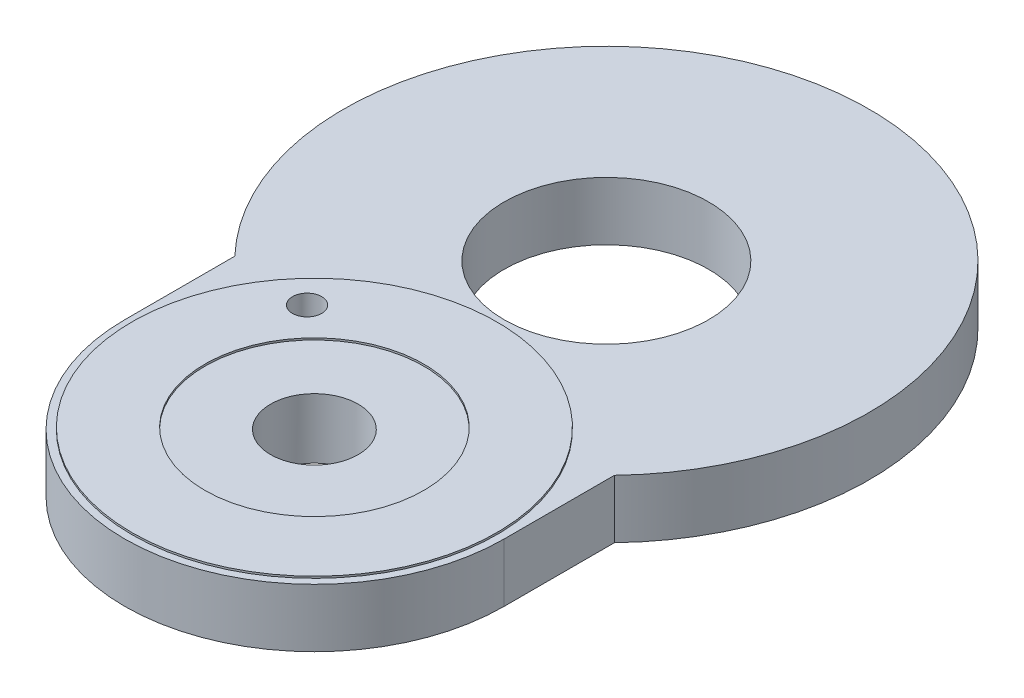
SolidWorks part; units mm, degrees
material "C110 COPPER"
ref_plane "Front Plane" through (0, 0, 0) normal (0, 0, 1) x (1, 0, 0)
ref_plane "Top Plane" through (0, 0, 0) normal (0, 1, 0) x (1, 0, 0)
ref_plane "Right Plane" through (0, 0, 0) normal (1, 0, 0) x (0, 0, -1)
sketch "Sketch1" plane through (0, 0, 0) normal (0, 1, 0) x (1, 0, 0)
  line L0 (0, -4.4244) -> (0, 10.7228) construction
  line L1 (-2.6, 0) -> (-2.6, 1.51)
  line L2 (2.6, 0) -> (2.6, 1.51)
  arc A0 (-2.6, 0) -> (2.6, 0) centre (0, 0) ccw
  arc A1 (2.6, 1.51) -> (-2.6, 1.51) centre (0, 4) ccw
  circle A2 centre (0, 4) radius 1.4
  dimension "D1" = 7.2
  dimension "D2" = 5.2
  dimension "D4" = 2.8
  dimension "D3" = 4
extrude "Boss-Extrude1" add sketch "Sketch1" along normal blind 0.8
sketch "Sketch2" plane through (0, 0.8, 0) normal (0, 1, 0) x (1, 0, 0)
  circle A0 centre (0, 0) radius 0.6
  circle A1 centre (-1.5, 1.4) radius 0.2
  dimension "D1" = 1.2
  dimension "D2" = 0.4
  dimension "D3" = 1.5
  dimension "D4" = 1.4
extrude "Cut-Extrude1" cut sketch "Sketch2" against normal blind 0.8
sketch "Sketch3" plane through (0, 0.8, 0) normal (0, 1, 0) x (1, 0, 0)
  circle A0 centre (0, 0) radius 1.5
  circle A1 centre (0, 0) radius 2.5
  circle A2 centre (-1.5, 1.4) radius 0.2 construction
  circle A3 centre (-1.5, 1.4) radius 0.2
  dimension "D1" = 3
  dimension "D2" = 5
extrude "Boss-Extrude2" add sketch "Sketch3" along normal blind 0.0254
sketch "Sketch4" plane through (0, 0, 0) normal (0, -1, 0) x (1, 0, 0)
  line L0 (0, -4.7101) -> (0, 2.7101) construction
  line L1 (0, -4) -> (-1.5, -1.4) construction
  circle A3 centre (0, -4) radius 1.4 construction
  circle A4 centre (0, -4) radius 1.4 construction
  arc A5 (-1.4992, -1.4014) -> (0, -1) centre (0, -4) ccw construction
  arc A6 (-1.7276, -1.0054) -> (0, -0.5428) centre (0, -4) ccw
  arc A7 (-1.2707, -1.7975) -> (0, -1.4572) centre (0, -4) ccw
  arc A8 (-1.2707, -1.7975) -> (-1.7276, -1.0054) centre (-1.4992, -1.4014) ccw
  arc A9 (0, -0.5428) -> (0, -1.4572) centre (0, -1) ccw
  circle A10 centre (-1.5, -1.4) radius 0.2 construction
  circle A11 centre (-1.5, -1.4) radius 0.2 construction
  circle A12 centre (0, 0) radius 1
  point P5 (0.776, -6.8979)
  circle M4 centre (0, 0) radius 0.6
  circle M5 centre (-1.5, -1.4) radius 0.2
  dimension "D1" = 0.9144
  dimension "D2" = 3
  dimension "D3" = 2
extrude "Boss-Extrude3" add sketch "Sketch4" along normal blind 0.0254 contours A6 A12 A9 M4 | A9 A12 A6 M4 | A12 A9 A7 A8 A6 M5
